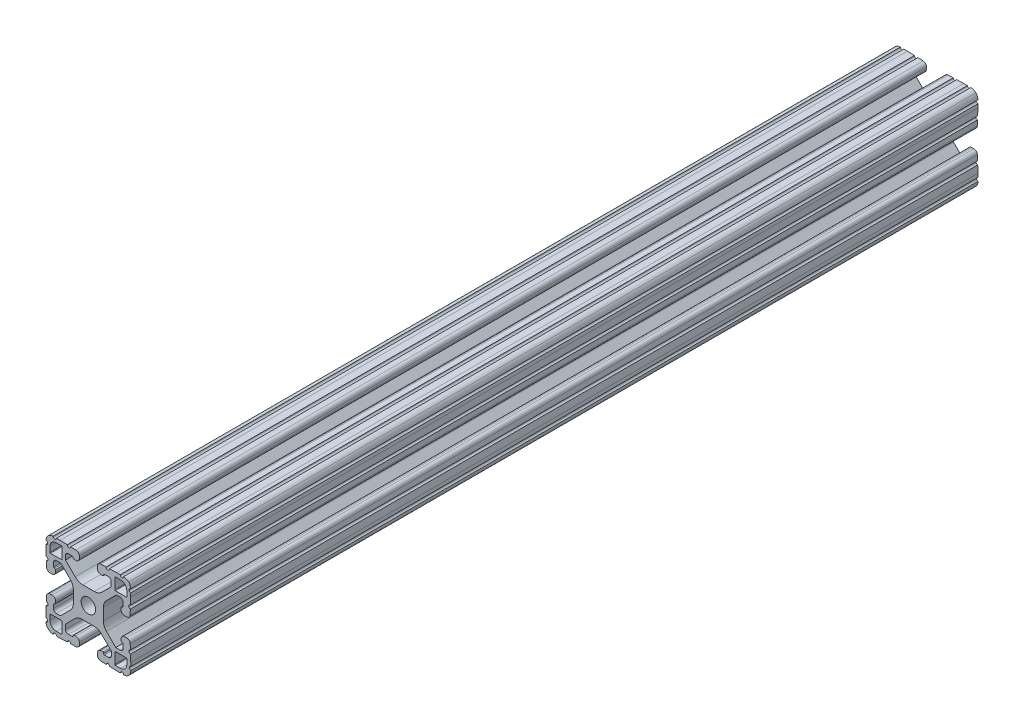
SolidWorks part; units mm, degrees
material "6061-T6 (SS)"
ref_plane "Front Plane" through (0, 0, 0) normal (0, 0, 1) x (1, 0, 0)
ref_plane "Top Plane" through (0, 0, 0) normal (0, 1, 0) x (1, 0, 0)
ref_plane "Right Plane" through (0, 0, 0) normal (1, 0, 0) x (0, 0, -1)
ref_plane "Plane1" through (0, 0, -25.4) normal (0, 0, -1) x (-1, 0, 0)
sketch "Sketch1" plane through (0, 0, -25.4) normal (0, 0, -1) x (-1, 0, 0)
  line L0 (-83.3577, 88.2941) -> (-83.3577, 93.1709)
  line L1 (-83.1037, 93.4249) -> (-80.767, 93.4249)
  line L2 (-77.9729, 90.6309) -> (-77.9729, 88.2941)
  line L3 (-78.2269, 88.0401) -> (-83.1037, 88.0401)
  line L4 (-83.3577, 59.2291) -> (-83.3577, 64.1059)
  line L5 (-83.1037, 64.3599) -> (-78.2269, 64.3599)
  line L6 (-77.9729, 64.1059) -> (-77.9729, 61.7691)
  line L7 (-80.767, 58.9751) -> (-83.1037, 58.9751)
  line L8 (-107.1423, 93.1709) -> (-107.1423, 88.2941)
  line L9 (-107.3963, 88.0401) -> (-112.2731, 88.0401)
  line L10 (-112.5271, 88.2941) -> (-112.5271, 90.6309)
  line L11 (-109.733, 93.4249) -> (-107.3963, 93.4249)
  line L12 (-107.1423, 64.1059) -> (-107.1423, 59.2291)
  line L13 (-107.3963, 58.9751) -> (-109.733, 58.9751)
  line L14 (-112.5271, 61.7691) -> (-112.5271, 64.1059)
  line L15 (-112.2731, 64.3599) -> (-107.3963, 64.3599)
  line L16 (-88.0437, 91.8626) -> (-86.2967, 91.9236)
  line L17 (-84.9824, 90.6544) -> (-84.9824, 88.8002)
  line L18 (-84.9824, 88.8002) -> (-89.3066, 84.476)
  line L19 (-92.7196, 83.0295) -> (-97.9616, 83.0295)
  line L20 (-101.3202, 84.4207) -> (-105.516, 88.6165)
  line L21 (-105.516, 88.6165) -> (-105.516, 90.7313)
  line L22 (-104.2017, 92.0006) -> (-102.4547, 91.9396)
  line L23 (-101.7262, 91.1059) -> (-100.9297, 91.0781)
  line L24 (-99.2999, 92.6519) -> (-99.2999, 93.5668)
  line L25 (-100.8197, 95.1407) -> (-103.2119, 95.2242)
  line L26 (-104.735, 95.2774) -> (-107.9359, 95.3892)
  line L27 (-107.9359, 95.3892) -> (-109.5615, 95.3892)
  line L28 (-114.2859, 90.6648) -> (-114.2859, 89.0392)
  line L29 (-114.2859, 89.0392) -> (-114.1741, 85.8383)
  line L30 (-114.1209, 84.3152) -> (-114.0374, 81.9231)
  line L31 (-112.4635, 80.4032) -> (-111.5486, 80.4032)
  line L32 (-109.9748, 82.033) -> (-110.0026, 82.8295)
  line L33 (-110.8377, 83.5577) -> (-110.8987, 85.3047)
  line L34 (-109.6294, 86.619) -> (-107.8072, 86.619)
  line L35 (-107.8072, 86.619) -> (-103.3649, 82.1768)
  line L36 (-101.9737, 78.8182) -> (-101.9737, 73.576)
  line L37 (-103.3649, 70.2174) -> (-107.5607, 66.0217)
  line L38 (-107.5607, 66.0217) -> (-109.6524, 66.0217)
  line L39 (-110.9217, 67.336) -> (-110.8607, 69.083)
  line L40 (-110.0322, 69.8124) -> (-110.0043, 70.6089)
  line L41 (-111.5782, 72.2387) -> (-112.4931, 72.2387)
  line L42 (-114.0669, 70.7189) -> (-114.1505, 68.3267)
  line L43 (-114.2036, 66.8036) -> (-114.3154, 63.6027)
  line L44 (-114.3154, 63.6027) -> (-114.3154, 61.9626)
  line L45 (-109.6111, 57.1437) -> (-107.9855, 57.1437)
  line L46 (-107.9855, 57.1437) -> (-104.7846, 57.2555)
  line L47 (-103.2615, 57.3086) -> (-100.8694, 57.3922)
  line L48 (-99.3495, 58.966) -> (-99.3495, 59.8809)
  line L49 (-100.9794, 61.4548) -> (-101.7758, 61.4269)
  line L50 (-102.5054, 60.599) -> (-104.2524, 60.538)
  line L51 (-105.5667, 61.8072) -> (-105.5667, 63.6295)
  line L52 (-105.5667, 63.6295) -> (-101.1311, 68.065)
  line L53 (-97.7725, 69.4562) -> (-92.5304, 69.4562)
  line L54 (-89.1717, 68.065) -> (-84.976, 63.8692)
  line L55 (-84.976, 63.8692) -> (-84.976, 61.7811)
  line L56 (-86.2903, 60.5118) -> (-88.0373, 60.5728)
  line L57 (-88.7596, 61.4332) -> (-89.5561, 61.461)
  line L58 (-91.1859, 59.8872) -> (-91.1859, 58.9723)
  line L59 (-89.6661, 57.3985) -> (-87.2739, 57.3149)
  line L60 (-85.7508, 57.2617) -> (-82.5499, 57.15)
  line L61 (-82.5499, 57.15) -> (-80.9244, 57.15)
  line L62 (-76.2, 61.8744) -> (-76.2, 63.4999)
  line L63 (-76.2, 63.4999) -> (-76.3117, 66.7008)
  line L64 (-76.3649, 68.2239) -> (-76.4484, 70.6161)
  line L65 (-78.0223, 72.1359) -> (-78.9372, 72.1359)
  line L66 (-80.511, 70.5061) -> (-80.4832, 69.7096)
  line L67 (-79.6552, 68.9801) -> (-79.5942, 67.2331)
  line L68 (-80.8634, 65.9188) -> (-82.6857, 65.9188)
  line L69 (-82.6857, 65.9188) -> (-87.1213, 70.3543)
  line L70 (-88.5125, 73.7128) -> (-88.5126, 78.955)
  line L71 (-87.1214, 82.3137) -> (-82.9257, 86.5095)
  line L72 (-82.9257, 86.5095) -> (-80.8375, 86.5095)
  line L73 (-79.5682, 85.1951) -> (-79.6293, 83.4482)
  line L74 (-80.4896, 82.7258) -> (-80.5175, 81.9294)
  line L75 (-78.9436, 80.2995) -> (-78.0287, 80.2995)
  line L76 (-76.4549, 81.8194) -> (-76.3713, 84.2115)
  line L77 (-76.3182, 85.7346) -> (-76.2064, 88.9355)
  line L78 (-76.2064, 88.9355) -> (-76.2064, 90.5611)
  line L79 (-80.9308, 95.2855) -> (-82.5564, 95.2855)
  line L80 (-82.5564, 95.2855) -> (-85.7573, 95.1737)
  line L81 (-87.2803, 95.1205) -> (-89.6725, 95.037)
  line L82 (-91.1924, 93.4632) -> (-91.1924, 92.5483)
  line L83 (-89.5625, 90.9744) -> (-88.7661, 91.0023)
  arc A0 (-83.3577, 93.1709) -> (-83.1037, 93.4249) centre (-83.1037, 93.1709) cw
  arc A1 (-80.767, 93.4249) -> (-77.9729, 90.6309) centre (-80.7669, 90.6309) cw
  arc A2 (-77.9729, 88.2941) -> (-78.2269, 88.0401) centre (-78.2269, 88.2941) cw
  arc A3 (-83.1037, 88.0401) -> (-83.3577, 88.2941) centre (-83.1037, 88.2941) cw
  arc A4 (-83.1037, 58.9751) -> (-83.3577, 59.2291) centre (-83.1037, 59.2291) cw
  arc A5 (-83.3577, 64.1059) -> (-83.1037, 64.3599) centre (-83.1037, 64.1059) cw
  arc A6 (-78.2269, 64.3599) -> (-77.9729, 64.1059) centre (-78.2269, 64.1059) cw
  arc A7 (-77.9729, 61.7691) -> (-80.767, 58.9751) centre (-80.7669, 61.7691) cw
  arc A8 (-107.3963, 93.4249) -> (-107.1423, 93.1709) centre (-107.3963, 93.1709) cw
  arc A9 (-107.1423, 88.2941) -> (-107.3963, 88.0401) centre (-107.3963, 88.2941) cw
  arc A10 (-112.2731, 88.0401) -> (-112.5271, 88.2941) centre (-112.2731, 88.2941) cw
  arc A11 (-112.5271, 90.6309) -> (-109.733, 93.4249) centre (-109.7331, 90.6309) cw
  arc A12 (-107.1423, 59.2291) -> (-107.3963, 58.9751) centre (-107.3963, 59.2291) cw
  arc A13 (-109.733, 58.9751) -> (-112.5271, 61.7691) centre (-109.7331, 61.7691) cw
  arc A14 (-112.5271, 64.1059) -> (-112.2731, 64.3599) centre (-112.2731, 64.1059) cw
  arc A15 (-107.3963, 64.3599) -> (-107.1423, 64.1059) centre (-107.3963, 64.1059) cw
  circle A16 centre (-95.25, 76.2) radius 3.2639
  arc A17 (-88.7661, 91.0023) -> (-88.3984, 91.383) centre (-88.7794, 91.383) ccw
  arc A18 (-88.3984, 91.383) -> (-88.0437, 91.8626) centre (-88.0304, 91.4819) cw
  arc A19 (-86.2967, 91.9236) -> (-84.9824, 90.6544) centre (-86.2524, 90.6544) cw
  arc A20 (-89.3066, 84.476) -> (-92.7196, 83.0295) centre (-92.7196, 87.7793) cw
  arc A21 (-97.9616, 83.0295) -> (-101.3202, 84.4207) centre (-97.9616, 87.7793) cw
  arc A22 (-105.516, 90.7313) -> (-104.2017, 92.0006) centre (-104.246, 90.7313) cw
  arc A23 (-102.4547, 91.9396) -> (-102.087, 91.5588) centre (-102.468, 91.5588) cw
  arc A24 (-102.087, 91.5588) -> (-101.7262, 91.1059) centre (-101.7129, 91.4867) ccw
  arc A25 (-100.9297, 91.0781) -> (-99.2999, 92.6519) centre (-100.8747, 92.6519) ccw
  arc A26 (-99.2999, 93.5668) -> (-100.8197, 95.1407) centre (-100.8747, 93.5668) ccw
  arc A27 (-103.2119, 95.2242) -> (-104.735, 95.2774) centre (-103.9735, 95.2508) cw
  arc A28 (-109.5615, 95.3892) -> (-111.0855, 95.3892) centre (-110.3235, 95.3892) cw
  arc A29 (-111.0855, 95.3892) -> (-113.3432, 94.4465) centre (-111.0855, 92.2142) ccw
  arc A30 (-113.3432, 94.4465) -> (-114.2859, 92.1888) centre (-111.1109, 92.1888) ccw
  arc A31 (-114.2859, 92.1888) -> (-114.2859, 90.6648) centre (-114.2859, 91.4268) cw
  arc A32 (-114.1741, 85.8383) -> (-114.1209, 84.3152) centre (-114.1475, 85.0768) cw
  arc A33 (-114.0374, 81.9231) -> (-112.4635, 80.4032) centre (-112.4635, 81.978) ccw
  arc A34 (-111.5486, 80.4032) -> (-109.9748, 82.033) centre (-111.5486, 81.978) ccw
  arc A35 (-110.0026, 82.8295) -> (-110.3834, 83.1972) centre (-110.3834, 82.8162) ccw
  arc A36 (-110.3834, 83.1972) -> (-110.8377, 83.5577) centre (-110.4569, 83.571) cw
  arc A37 (-110.8987, 85.3047) -> (-109.6294, 86.619) centre (-109.6294, 85.349) cw
  arc A38 (-103.3649, 82.1768) -> (-101.9737, 78.8182) centre (-106.7235, 78.8182) cw
  arc A39 (-101.9737, 73.576) -> (-103.3649, 70.2174) centre (-106.7235, 73.576) cw
  arc A40 (-109.6524, 66.0217) -> (-110.9217, 67.336) centre (-109.6524, 67.2917) cw
  arc A41 (-110.8607, 69.083) -> (-110.4799, 69.4507) centre (-110.4799, 69.0697) cw
  arc A42 (-110.4799, 69.4507) -> (-110.0322, 69.8124) centre (-110.413, 69.8257) ccw
  arc A43 (-110.0043, 70.6089) -> (-111.5782, 72.2387) centre (-111.5782, 70.6639) ccw
  arc A44 (-112.4931, 72.2387) -> (-114.0669, 70.7189) centre (-112.4931, 70.6639) ccw
  arc A45 (-114.1505, 68.3267) -> (-114.2036, 66.8036) centre (-114.1771, 67.5652) cw
  arc A46 (-114.3154, 61.9626) -> (-114.3332, 60.4644) centre (-114.4639, 61.2152) cw
  arc A47 (-114.3332, 60.4644) -> (-113.3928, 58.0864) centre (-111.1605, 60.3441) ccw
  arc A48 (-113.3928, 58.0864) -> (-111.1351, 57.1437) centre (-111.1351, 60.3187) ccw
  arc A49 (-111.1351, 57.1437) -> (-109.6111, 57.1437) centre (-110.3731, 57.1437) cw
  arc A50 (-104.7846, 57.2555) -> (-103.2615, 57.3086) centre (-104.0231, 57.2821) cw
  arc A51 (-100.8694, 57.3922) -> (-99.3495, 58.966) centre (-100.9243, 58.966) ccw
  arc A52 (-99.3495, 59.8809) -> (-100.9794, 61.4548) centre (-100.9243, 59.8809) ccw
  arc A53 (-101.7758, 61.4269) -> (-102.1435, 61.0462) centre (-101.7625, 61.0462) ccw
  arc A54 (-102.1435, 61.0462) -> (-102.5054, 60.599) centre (-102.5187, 60.9797) cw
  arc A55 (-104.2524, 60.538) -> (-105.5667, 61.8072) centre (-104.2967, 61.8072) cw
  arc A56 (-101.1311, 68.065) -> (-97.7725, 69.4562) centre (-97.7725, 64.7064) cw
  arc A57 (-92.5304, 69.4562) -> (-89.1717, 68.065) centre (-92.5304, 64.7064) cw
  arc A58 (-84.976, 61.7811) -> (-86.2903, 60.5118) centre (-86.246, 61.7811) cw
  arc A59 (-88.0373, 60.5728) -> (-88.405, 60.9536) centre (-88.024, 60.9536) cw
  arc A60 (-88.405, 60.9536) -> (-88.7596, 61.4332) centre (-88.7729, 61.0524) ccw
  arc A61 (-89.5561, 61.461) -> (-91.1859, 59.8872) centre (-89.6111, 59.8872) ccw
  arc A62 (-91.1859, 58.9723) -> (-89.6661, 57.3985) centre (-89.6111, 58.9723) ccw
  arc A63 (-87.2739, 57.3149) -> (-85.7508, 57.2617) centre (-86.5124, 57.2883) cw
  arc A64 (-80.9244, 57.15) -> (-79.4004, 57.15) centre (-80.1624, 57.15) cw
  arc A65 (-79.4004, 57.15) -> (-77.1426, 58.0927) centre (-79.4004, 60.325) ccw
  arc A66 (-77.1426, 58.0927) -> (-76.2, 60.3504) centre (-79.375, 60.3504) ccw
  arc A67 (-76.2, 60.3504) -> (-76.2, 61.8744) centre (-76.2, 61.1124) cw
  arc A68 (-76.3117, 66.7008) -> (-76.3649, 68.2239) centre (-76.3383, 67.4624) cw
  arc A69 (-76.4484, 70.6161) -> (-78.0223, 72.1359) centre (-78.0223, 70.5611) ccw
  arc A70 (-78.9372, 72.1359) -> (-80.511, 70.5061) centre (-78.9372, 70.5611) ccw
  arc A71 (-80.4832, 69.7096) -> (-80.1024, 69.342) centre (-80.1024, 69.723) ccw
  arc A72 (-80.1024, 69.342) -> (-79.6552, 68.9801) centre (-80.036, 68.9668) cw
  arc A73 (-79.5942, 67.2331) -> (-80.8634, 65.9188) centre (-80.8634, 67.1888) cw
  arc A74 (-87.1213, 70.3543) -> (-88.5125, 73.7128) centre (-83.7627, 73.7129) cw
  arc A75 (-88.5126, 78.955) -> (-87.1214, 82.3137) centre (-83.7628, 78.9551) cw
  arc A76 (-80.8375, 86.5095) -> (-79.5682, 85.1951) centre (-80.8375, 85.2395) cw
  arc A77 (-79.6293, 83.4482) -> (-80.01, 83.0805) centre (-80.01, 83.4615) cw
  arc A78 (-80.01, 83.0805) -> (-80.4896, 82.7258) centre (-80.1089, 82.7125) ccw
  arc A79 (-80.5175, 81.9294) -> (-78.9436, 80.2995) centre (-78.9436, 81.8743) ccw
  arc A80 (-78.0287, 80.2995) -> (-76.4549, 81.8194) centre (-78.0287, 81.8743) ccw
  arc A81 (-76.3713, 84.2115) -> (-76.3182, 85.7346) centre (-76.3448, 84.9731) cw
  arc A82 (-76.2064, 90.5611) -> (-76.2064, 92.0851) centre (-76.2064, 91.3231) cw
  arc A83 (-76.2064, 92.0851) -> (-77.1491, 94.3428) centre (-79.3814, 92.0851) ccw
  arc A84 (-77.1491, 94.3428) -> (-79.4068, 95.2855) centre (-79.4068, 92.1105) ccw
  arc A85 (-79.4068, 95.2855) -> (-80.9308, 95.2855) centre (-80.1688, 95.2855) cw
  arc A86 (-85.7573, 95.1737) -> (-87.2803, 95.1205) centre (-86.5188, 95.1471) cw
  arc A87 (-89.6725, 95.037) -> (-91.1924, 93.4632) centre (-89.6176, 93.4632) ccw
  arc A88 (-91.1924, 92.5483) -> (-89.5625, 90.9744) centre (-89.6176, 92.5483) ccw
extrude "Boss-Extrude1" add sketch "Sketch1" against normal blind 381
